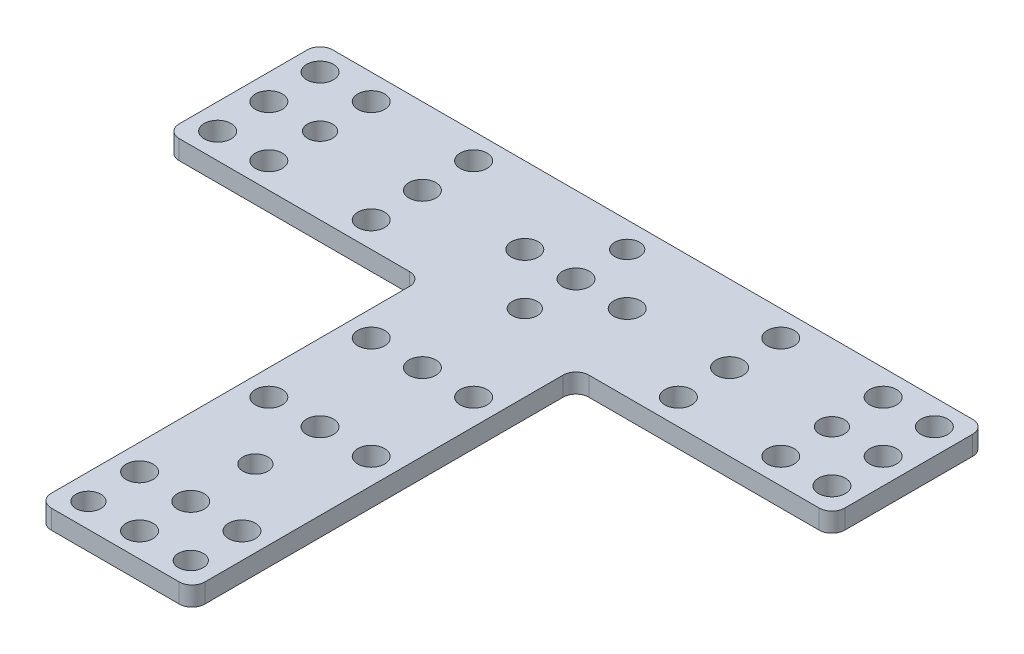
SolidWorks part; units mm, degrees
ref_plane "Front Plane" through (0, 0, 0) normal (0, 0, 1) x (1, 0, 0)
ref_plane "Top Plane" through (0, 0, 0) normal (0, 1, 0) x (1, 0, 0)
ref_plane "Right Plane" through (0, 0, 0) normal (1, 0, 0) x (0, 0, -1)
sketch "Sketch1" plane through (0, 0, 0) normal (0, 1, 0) x (1, 0, 0)
  line L0 (12, 0) -> (52, 0)
  line L1 (-52, 24) -> (52, 24)
  line L2 (-52, 24) -> (-52, 0)
  line L3 (-52, 0) -> (-12, 0)
  line L4 (52, 24) -> (52, 0)
  line L6 (-12, 0) -> (-12, -60)
  line L7 (-12, -60) -> (12, -60)
  line L8 (12, 0) -> (12, -60)
  point P10 (0, 24)
  dimension "D1" = 24
  dimension "D2" = 24
  dimension "D3" = 84
  dimension "D4" = 104
extrude "Boss-Extrude1" add sketch "Sketch1" along normal blind 3
sketch "Sketch2" plane through (0, 3, 0) normal (0, 1, 0) x (1, 0, 0)
  line L0 (-52, 12) -> (52, 12) construction
  line L1 (-52, 24) -> (-52, 0) construction
  line L2 (52, 0) -> (52, 24) construction
  line L3 (0, 24) -> (0, -60) construction
  line L4 (52, 24) -> (-52, 24) construction
  line L5 (-12, -60) -> (12, -60) construction
  line L6 (-52, 20) -> (52, 20) construction
  line L7 (-48, 12) -> (-48, 20) construction
  line L8 (-40, 20) -> (-40, 12) construction
  line L9 (-24, 12) -> (-24, 20) construction
  line L10 (-8, -60) -> (-8, 24) construction
  line L11 (-8, -12) -> (0, -12) construction
  line L12 (0, -28) -> (-8, -28) construction
  line L13 (-8, -48.2) -> (0, -48.2) construction
  line L14 (0, -56.2) -> (-8, -56.2) construction
  line L15 (24, 12) -> (24, 20) construction
  line L16 (40, 20) -> (40, 12) construction
  line L17 (48, 12) -> (48, 20) construction
  circle A0 centre (0, 12) radius 2.1
  circle A2 centre (-8, 12) radius 2.1
  circle A3 centre (0, 20) radius 1.95
  circle A4 centre (-48, 12) radius 2.1
  circle A5 centre (-48, 20) radius 2.1
  circle A6 centre (-40, 12) radius 1.95
  circle A7 centre (-40, 20) radius 2.1
  circle A8 centre (-24, 12) radius 2.1
  circle A9 centre (-24, 20) radius 2.1
  circle A10 centre (0, -12) radius 2.1
  circle A11 centre (0, -28) radius 2.1
  circle A12 centre (0, -38.1) radius 1.95
  circle A13 centre (0, -48.2) radius 2.1
  circle A14 centre (0, -56.2) radius 2.1
  circle A15 centre (-8, -56.2) radius 1.95
  circle A16 centre (-8, -48.2) radius 2.1
  circle A18 centre (-8, -28) radius 2.1
  circle A19 centre (-8, -12) radius 2.1
  circle A20 centre (0, 4) radius 1.95
  circle A21 centre (-24, 4) radius 2.1
  circle A22 centre (-40, 4) radius 2.1
  circle A23 centre (-48, 4) radius 2.1
  circle A24 centre (8, -56.2) radius 1.95
  circle A25 centre (8, -48.2) radius 2.1
  circle A26 centre (8, -28) radius 2.1
  circle A27 centre (8, -12) radius 2.1
  circle A28 centre (8, 12) radius 2.1
  circle A29 centre (24, 4) radius 2.1
  circle A30 centre (24, 20) radius 2.1
  circle A31 centre (24, 12) radius 2.1
  circle A32 centre (40, 20) radius 2.1
  circle A33 centre (40, 12) radius 1.95
  circle A34 centre (48, 12) radius 2.1
  circle A35 centre (40, 4) radius 2.1
  circle A36 centre (48, 4) radius 2.1
  circle A37 centre (48, 20) radius 2.1
  dimension "D1" = 4.2
  dimension "D6" = 3.9
  dimension "D4" = 16
  dimension "D8" = 16
  dimension "D2" = 8
  dimension "D3" = 16
  dimension "D5" = 16
  dimension "D7" = 16
  dimension "D9" = 8
  dimension "D10" = 24
  dimension "D11" = 16
  dimension "D12" = 16
  dimension "D13" = 8
extrude "Cut-Extrude1" cut sketch "Sketch2" against normal through all
fillet "Fillet1" radius 2 8 edges at (52, 1.5, -24) (52, 1.5, 0) (12, 1.5, 0) (12, 1.5, 60) (-12, 1.5, 60) (-12, 1.5, 0) (-52, 1.5, -24) (-52, 1.5, 0)
equation "\"width\"= 24"
equation "\"thk\"= 3"
equation "\"holesize\"= 4.2"
equation "\"holedistance\"= ( 20 + 12 ) / 2"
equation "\"D1@Sketch2\"=\"holesize\""
equation "\"D4@Sketch2\"=\"holedistance\""
equation "\"D2@Sketch2\"=\"holedistance\"/2"
equation "\"D3@Sketch2\"=\"holedistance\""
equation "\"D5@Sketch2\"=\"holedistance\""
equation "\"threaded_hole\"= 3.9"
equation "\"D6@Sketch2\"=\"threaded_hole\""
equation "\"D7@Sketch2\"=\"holedistance\""
equation "\"D9@Sketch2\"=\"holedistance\"/2"
equation "\"D10@Sketch2\"=\"holedistance\"*1.5"
equation "\"D11@Sketch2\"=\"holedistance\""
equation "\"D13@Sketch2\"=\"D12@Sketch2\"/2"
equation "\"fillet_radius\"= 2"
equation "\"D1@Fillet1\"=\"fillet_radius\""
equation "\"ground_clearance\"= 25"
equation "\"tire_thk\"= 3"
equation "\"innerwheel_diam\" = \"wheel_diam\"-2*\"tire_thk\""
equation "\"innerwheel_thk\"= 8"
equation "\"wheel_diam\"= 2*(\"width\"/2+\"ground_clearance\")"
equation "\"coloursensor_holesize\"= 2.65"
equation "\"hole_to_edge\" = 4"
